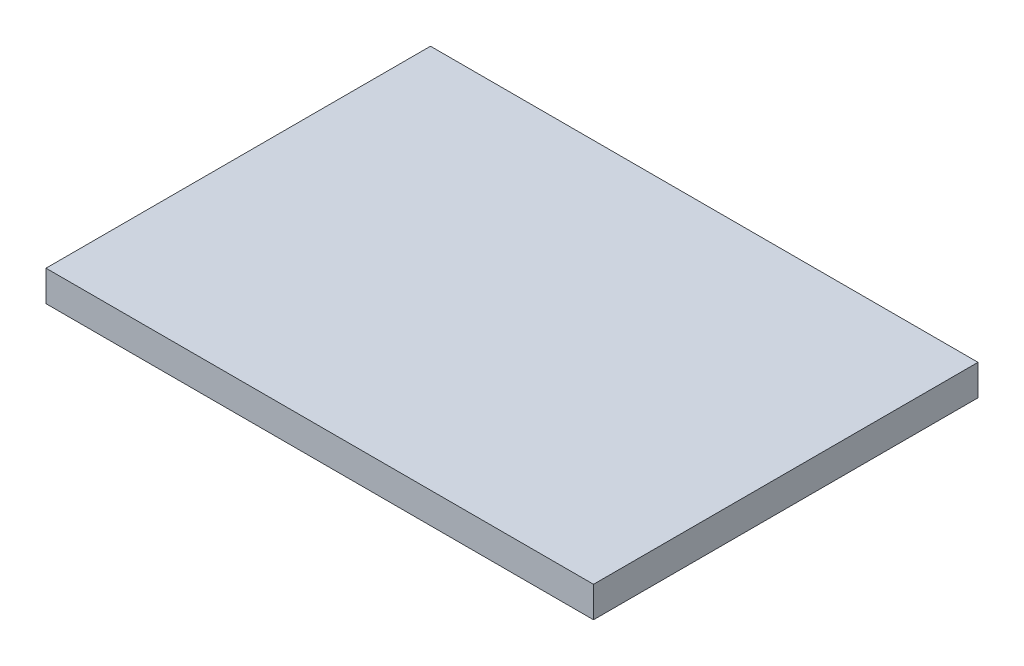
SolidWorks part; units mm, degrees
ref_plane "Front Plane" through (0, 0, 0) normal (0, 0, 1) x (1, 0, 0)
ref_plane "Top Plane" through (0, 0, 0) normal (0, 1, 0) x (1, 0, 0)
ref_plane "Right Plane" through (0, 0, 0) normal (1, 0, 0) x (0, 0, -1)
sketch "Sketch1" plane through (0, 0, 0) normal (0, 1, 0) x (1, 0, 0)
  line L1 (-28.3144, 6.8688) -> (7.2856, 6.8688)
  line L2 (-28.3144, 6.8688) -> (-28.3144, -18.1312)
  line L3 (-28.3144, -18.1312) -> (7.2856, -18.1312)
  line L4 (7.2856, 6.8688) -> (7.2856, -18.1312)
  dimension "D1" = 25
  dimension "D2" = 35.6
extrude "Boss-Extrude1" add sketch "Sketch1" along normal blind 2
